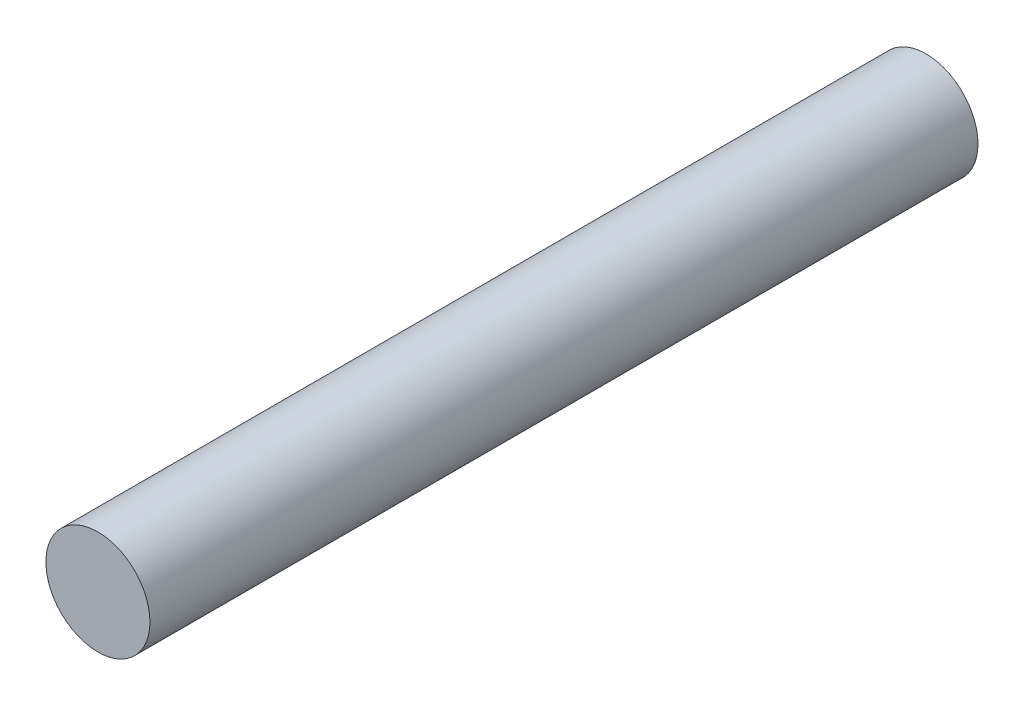
SolidWorks part; units mm, degrees
material "6061-T6 (SS)"
ref_plane "Front Plane" through (0, 0, 0) normal (0, 0, 1) x (1, 0, 0)
ref_plane "Top Plane" through (0, 0, 0) normal (0, 1, 0) x (1, 0, 0)
ref_plane "Right Plane" through (0, 0, 0) normal (1, 0, 0) x (0, 0, -1)
sketch "Sketch1" plane through (0, 0, 0) normal (0, 0, 1) x (1, 0, 0)
  circle A0 centre (0, 0) radius 3.175
  dimension "D1" = 6.35
extrude "Boss-Extrude1" add sketch "Sketch1" along normal blind 50.5295
